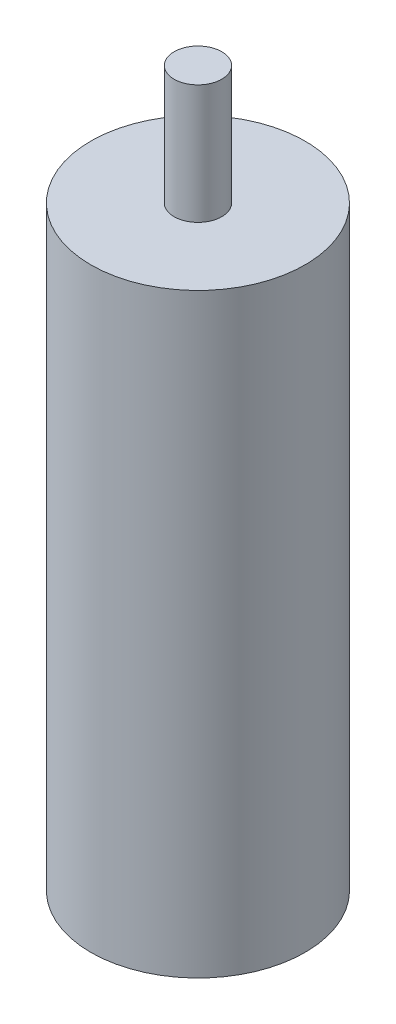
SolidWorks part; units mm, degrees
ref_plane "Front Plane" through (0, 0, 0) normal (0, 0, 1) x (1, 0, 0)
ref_plane "Top Plane" through (0, 0, 0) normal (0, 1, 0) x (1, 0, 0)
ref_plane "Right Plane" through (0, 0, 0) normal (1, 0, 0) x (0, 0, -1)
sketch "Sketch1" plane through (0, 0, 0) normal (0, 1, 0) x (1, 0, 0)
  circle A0 centre (0, 0) radius 22.5
extrude "Boss-Extrude1" add sketch "Sketch1" along normal blind 125
sketch "Sketch2" plane through (0, 125, 0) normal (0, 1, 0) x (1, 0, 0)
  circle A0 centre (0, 0) radius 5
extrude "Boss-Extrude2" add sketch "Sketch2" along normal blind 25
